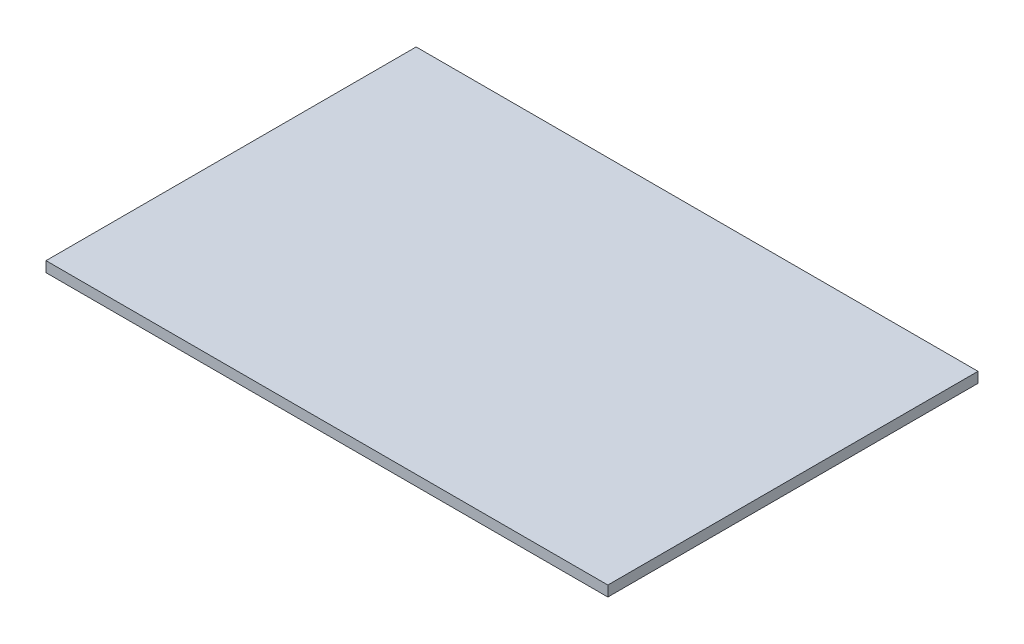
SolidWorks part; units mm, degrees
ref_plane "Front Plane" through (0, 0, 0) normal (0, 0, 1) x (1, 0, 0)
ref_plane "Top Plane" through (0, 0, 0) normal (0, 1, 0) x (1, 0, 0)
ref_plane "Right Plane" through (0, 0, 0) normal (1, 0, 0) x (0, 0, -1)
sketch "Sketch1" plane through (0, 0, 0) normal (0, 1, 0) x (1, 0, 0)
  line L1 (539.75, -355.6) -> (-539.75, -355.6)
  line L2 (539.75, -355.6) -> (539.75, 355.6)
  line L3 (539.75, 355.6) -> (-539.75, 355.6)
  line L4 (-539.75, -355.6) -> (-539.75, 355.6)
  line L5 (539.75, -355.6) -> (-539.75, 355.6) construction
  line L6 (539.75, 355.6) -> (-539.75, -355.6) construction
  point P0 (0, 0)
  dimension "D1" = 1079.5
  dimension "D2" = 711.2
extrude "Boss-Extrude1" add sketch "Sketch1" along normal blind 20.066
